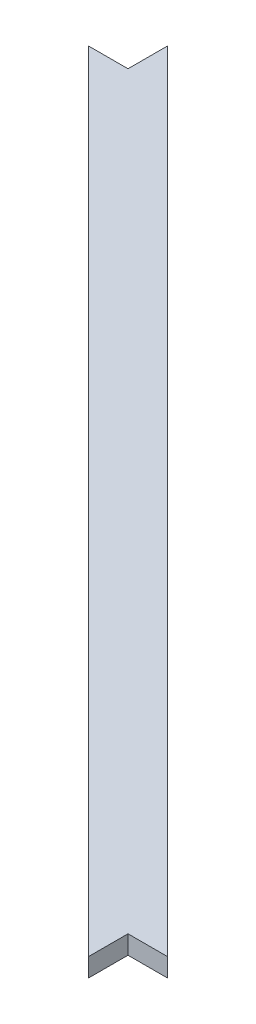
SolidWorks part; units mm, degrees
ref_plane "Front Plane" through (0, 0, 0) normal (0, 0, 1) x (1, 0, 0)
ref_plane "Top Plane" through (0, 0, 0) normal (0, 1, 0) x (1, 0, 0)
ref_plane "Right Plane" through (0, 0, 0) normal (1, 0, 0) x (0, 0, -1)
sketch "Sketch1" plane through (0, 0, 0) normal (0, 1, 0) x (1, 0, 0)
  line L0 (242.5296, -269.4704) -> (269.4704, -242.5296) construction
  line L5 (-294.1, -294.1) -> (294.1, -294.1) construction
  line L6 (-294.1, -294.1) -> (-294.1, 294.1) construction
  line L15 (-294.1, 294.1) -> (294.1, 294.1) construction
  line L16 (294.1, -294.1) -> (294.1, 294.1) construction
  line L23 (-294.1, -294.1) -> (294.1, 294.1) construction
  line L24 (-294.1, 294.1) -> (294.1, -294.1) construction
  line L25 (-294.1, 294.1) -> (-256, 294.1) construction
  line L26 (-294.1, 294.1) -> (-294.1, 256) construction
  line L27 (-294.1, 256) -> (-256, 256) construction
  line L28 (-256, 294.1) -> (-256, 256) construction
  line L29 (294.1, -294.1) -> (256, -294.1) construction
  line L30 (294.1, -294.1) -> (294.1, -256) construction
  line L31 (294.1, -256) -> (256, -256) construction
  line L32 (256, -294.1) -> (256, -256) construction
  line L33 (394.4204, -367.4796) -> (311.3933, -284.4525) construction
  line L34 (242.5296, -269.4704) -> (201.7372, -228.6779) construction
  line L35 (-256, 282.9408) -> (-256, 256)
  line L36 (-256, 256) -> (-282.9408, 256)
  line L37 (-282.9408, 256) -> (256, -282.9408)
  line L38 (256, -282.9408) -> (256, -256)
  line L39 (256, -256) -> (282.9408, -256)
  line L40 (282.9408, -256) -> (-256, 282.9408)
  point P0 (0, 0)
  point P3 (0, 0)
  point P16 (256, -256)
  point P19 (256, -282.9408)
  point P21 (282.9408, -256)
  point P22 (-282.9408, 256)
  point P23 (-256, 282.9408)
  dimension "D1" = 588.2
  dimension "D2" = 588.2
  dimension "D3" = 38.1
  dimension "D4" = 38.1
  dimension "D5" = 38.1
  dimension "D6" = 38.1
extrude "Boss-Extrude1" add sketch "Sketch1" along normal blind 12.7
